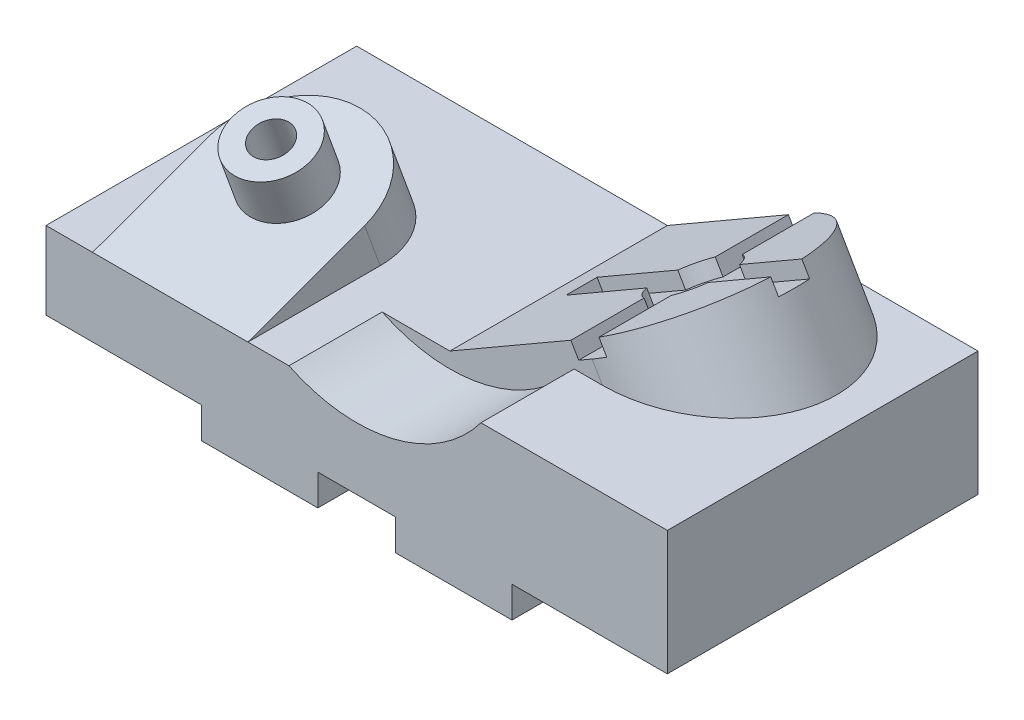
SolidWorks part; units mm, degrees
ref_plane "Alzado" through (0, 0, 0) normal (0, 0, 1) x (1, 0, 0)
ref_plane "Planta" through (0, 0, 0) normal (0, 1, 0) x (1, 0, 0)
ref_plane "Vista lateral" through (0, 0, 0) normal (1, 0, 0) x (0, 0, -1)
sketch "Croquis1" plane through (0, 0, 0) normal (0, 0, 1) x (1, 0, 0)
  line L0 (0, 0) -> (0, 25)
  line L1 (0, 25) -> (100, 25)
  line L2 (100, 25) -> (100, 40)
  line L3 (100, 40) -> (200, 40)
  line L4 (200, 40) -> (200, 0)
  line L5 (200, 0) -> (150, 0)
  line L6 (150, 0) -> (150, -10)
  line L7 (150, -10) -> (112.5, -10)
  line L8 (112.5, -10) -> (112.5, 0)
  line L9 (112.5, 0) -> (87.5, 0)
  line L10 (87.5, 0) -> (87.5, -10)
  line L11 (87.5, -10) -> (50, -10)
  line L12 (50, -10) -> (50, 0)
  line L13 (50, 0) -> (0, 0)
  dimension "D1" = 25
  dimension "D2" = 100
  dimension "D3" = 200
  dimension "D4" = 40
  dimension "D5" = 50
  dimension "D6" = 37.5
  dimension "D7" = 25
  dimension "D8" = 10
  dimension "D9" = 50
extrude "Saliente-Extruir1" add sketch "Croquis1" along normal mid plane 100
sketch "Croquis2" plane through (0, 0, 50) normal (0, 0, 1) x (1, 0, 0)
  line L0 (78.2055, 25) -> (100, 25)
  line L1 (100, 25) -> (0, 25) construction
  line L2 (100, 25) -> (100, 40)
  line L3 (100, 40) -> (140, 40)
  line L4 (200, 40) -> (100, 40) construction
  line L5 (200, 0) -> (200, 40) construction
  arc A0 (78.2055, 25) -> (140, 40) centre (100, 70) ccw
  dimension "D3" = 50
  dimension "D1" = 60
  dimension "D2" = 5
extrude "Cortar-Extruir1" cut sketch "Croquis2" against normal blind 30
ref_plane "Plano1" through (0, 38.1452, 13.8837) normal (0, 0.9397, 0.342) x (-1, 0, 0)
sketch "Croquis3" plane through (0, 38.1452, 13.8837) normal (0, 0.9397, 0.342) x (-1, 0, 0)
  line L0 (-15, 38.4341) -> (-15, -1.5659)
  line L1 (-78.2055, 38.4341) -> (0, 38.4341) construction
  line L2 (0, 38.4341) -> (0, -55.5351) construction
  line L3 (-65, -1.5659) -> (-65, 38.4341)
  line L4 (-65, 38.4341) -> (-15, 38.4341)
  arc A0 (-65, -1.5659) -> (-15, -1.5659) centre (-40, -1.5659) ccw
  dimension "D1" = 15
  dimension "D2" = 40
  dimension "D3" = 50
extrude "Saliente-Extruir2" add sketch "Croquis3" against normal up to surface up to face at (59.4018, 25, 6.6667)
sketch "Croquis4" plane through (0, 38.1452, 13.8837) normal (0, 0.9397, 0.342) x (1, 0, 0)
  circle A0 centre (40, 1.5659) radius 6
  circle A1 centre (40, 1.5659) radius 12.5
  dimension "D1" = 25
  dimension "D2" = 12
extrude "Saliente-Extruir3" add sketch "Croquis4" along normal blind 15
sketch "Croquis5" plane through (0, 38.1452, 13.8837) normal (0, 0.9397, 0.342) x (-1, 0, 0)
  circle A0 centre (-40, -1.5659) radius 6 construction
  circle A1 centre (-40, -1.5659) radius 6
extrude "Cortar-Extruir2" cut sketch "Croquis5" against normal through all
sketch "Croquis6" plane through (0, 0, 50) normal (0, 0, 1) x (1, 0, 0)
  line L0 (100, 25) -> (100, 40)
  line L1 (100, 40) -> (125.9808, 40)
  line L3 (100, 25) -> (125.9808, 40)
  line L4 (87.5, 0) -> (112.5, 0) construction
  dimension "D1" = 30
extrude "Cortar-Extruir3" cut sketch "Croquis6" against normal through all
sketch "Croquis7" plane through (14.1747, -24.5513, 0) normal (-0.5, 0.866, 0) x (0.866, 0.5, 0)
  line L1 (99.1025, 50) -> (149.1025, 50)
  line L2 (99.1025, 50) -> (99.1025, -20)
  line L3 (99.1025, -20) -> (149.1025, -20)
  arc A0 (149.1025, -20) -> (149.1025, 50) centre (149.1025, 15) ccw
  dimension "D1" = 50
  dimension "D2" = 70
extrude "Saliente-Extruir5" add sketch "Croquis7" against normal up to surface (11.547 mm away)
sketch "Croquis8" plane through (14.1747, -24.5513, 0) normal (-0.5, 0.866, 0) x (0.866, 0.5, 0)
  line L0 (149.1025, 15) -> (190.559, 15) construction
  line L1 (154.1025, 3.5436) -> (154.1025, -26.4564)
  line L2 (154.1025, -26.4564) -> (144.1025, -26.4564)
  line L3 (144.1025, 3.5436) -> (144.1025, -26.4564)
  line L4 (190.559, 20) -> (190.559, 10)
  line L5 (137.6461, 10) -> (107.6461, 10)
  line L6 (107.6461, 10) -> (107.6461, 20)
  line L7 (137.6461, 20) -> (107.6461, 20)
  line L8 (160.559, 10) -> (190.559, 10)
  line L9 (160.559, 20) -> (190.559, 20)
  line L10 (144.1025, 26.4564) -> (144.1025, 56.4564)
  line L11 (144.1025, 56.4564) -> (154.1025, 56.4564)
  line L12 (154.1025, 26.4564) -> (154.1025, 56.4564)
  arc A0 (160.559, 20) -> (154.1025, 26.4564) centre (149.1025, 15) ccw
  arc A1 (144.1025, 26.4564) -> (137.6461, 20) centre (149.1025, 15) ccw
  arc A2 (137.6461, 10) -> (144.1025, 3.5436) centre (149.1025, 15) ccw
  arc A3 (154.1025, 3.5436) -> (160.559, 10) centre (149.1025, 15) ccw
  point P22 (149.1025, 15)
  dimension "D1" = 25
  dimension "D2" = 10
  dimension "D3" = 30
  dimension "D4" = 4
extrude "Cortar-Extruir4" cut sketch "Croquis8" against normal blind 5
sketch "Croquis9" plane through (16.6747, -28.8814, 0) normal (-0.5, 0.866, 0) x (0.866, 0.5, 0)
  circle A0 centre (149.1025, 15) radius 7.5
  dimension "D1" = 15
extrude "Cortar-Extruir5" cut sketch "Croquis9" against normal through all
